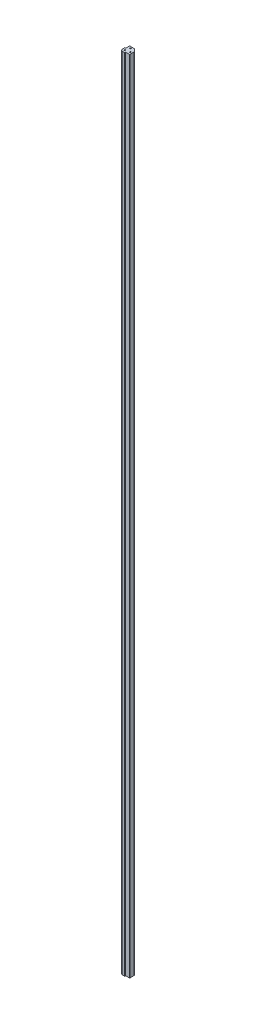
SolidWorks part; units mm, degrees
material "6063-T6"
ref_plane "Front" through (0, 0, 0) normal (0, 0, 1) x (1, 0, 0)
ref_plane "Top" through (0, 0, 0) normal (0, 1, 0) x (1, 0, 0)
ref_plane "Right" through (0, 0, 0) normal (1, 0, 0) x (0, 0, -1)
other "T1"
sketch "Sketch1" plane through (0, 0, 0) normal (0, 1, 0) x (1, 0, 0)
  line L0 (-3.048, 13.208) -> (-3.048, 4.953)
  line L1 (0, -5.08) -> (4.572, -5.08)
  line L2 (-5.08, 0) -> (-5.08, 4.572)
  line L3 (-2.286, 13.97) -> (7.3044, 13.97)
  line L4 (13.97, -2.286) -> (13.97, 7.3044)
  line L5 (13.208, -3.048) -> (4.953, -3.048)
  line L6 (4.826, -3.175) -> (4.826, -4.826)
  line L7 (-3.175, 4.826) -> (-4.826, 4.826)
  line L8 (7.8432, 13.7468) -> (13.7468, 7.8432)
  arc A0 (0, -5.08) -> (-5.08, 0) centre (0, 0) cw
  arc A1 (4.953, -3.048) -> (4.826, -3.175) centre (4.953, -3.175) ccw
  arc A2 (-3.048, 4.953) -> (-3.175, 4.826) centre (-3.175, 4.953) cw
  arc A3 (13.7468, 7.8432) -> (13.97, 7.3044) centre (13.208, 7.3044) cw
  arc A4 (7.8432, 13.7468) -> (7.3044, 13.97) centre (7.3044, 13.208) ccw
  arc A7 (13.208, -3.048) -> (13.97, -2.286) centre (13.208, -2.286) ccw
  arc A8 (-3.048, 13.208) -> (-2.286, 13.97) centre (-2.286, 13.208) cw
  arc A9 (4.826, -4.826) -> (4.572, -5.08) centre (4.572, -4.826) cw
  arc A10 (-4.826, 4.826) -> (-5.08, 4.572) centre (-4.826, 4.572) ccw
  point P0 (0, 0)
  point P20 (-3.048, 4.826)
  point P25 (7.62, 13.97)
  point P28 (-5.08, 4.826)
  point P35 (-3.048, 13.97)
  dimension "D3" = 5.08
  dimension "D8" = 0.127
  dimension "D9" = 0.762
  dimension "D10" = 0.254
  dimension "D2" = 19.05
  dimension "D4" = 6.35
  dimension "D5" = 45
  dimension "D6" = 2.032
  dimension "D7" = 9.144
extrude "Boss-Extrude1" add sketch "Sketch1" along normal blind 1828.8
hole_wizard "THRU HOLES" positions "Sketch2" profile "Sketch3" hole size "#6-32" standard "ANSI Inch" end condition through all
sketch "Sketch2" plane through (0, 1828.8, 0) normal (0, 1, 0) x (1, 0, 0)
  line L12 (7.3044, 13.97) -> (-2.286, 13.97) construction
  line L16 (2.54, 10.16) -> (10.16, 2.54) construction
  line L18 (-5.08, 4.572) -> (-5.08, 0) construction
  line L19 (13.7468, 7.8432) -> (7.8432, 13.7468) construction
  line L20 (6.35, 6.35) -> (0, 0) construction
  point P0 (0, 0)
  point P4 (2.54, 10.16)
  point P6 (10.16, 2.54)
  dimension "D1" = 7.62
  dimension "D2" = 3.81
sketch "Sketch3" plane through (0, 1828.8, 0) normal (1, 0, 0) x (0, 0, 1)
  line L0 (0, 0) -> (0, 1828.8)
  line L1 (0, 1828.8) -> (1.397, 1828.8)
  line L2 (1.397, 1828.8) -> (1.397, 0)
  line L5 (1.397, 0) -> (0, 0)
  line L11 (0, -6.35) -> (0, 107.95) construction
  dimension "Thru Hole Dia." = 2.794
  dimension "Thru Hole Depth" = 1828.8
